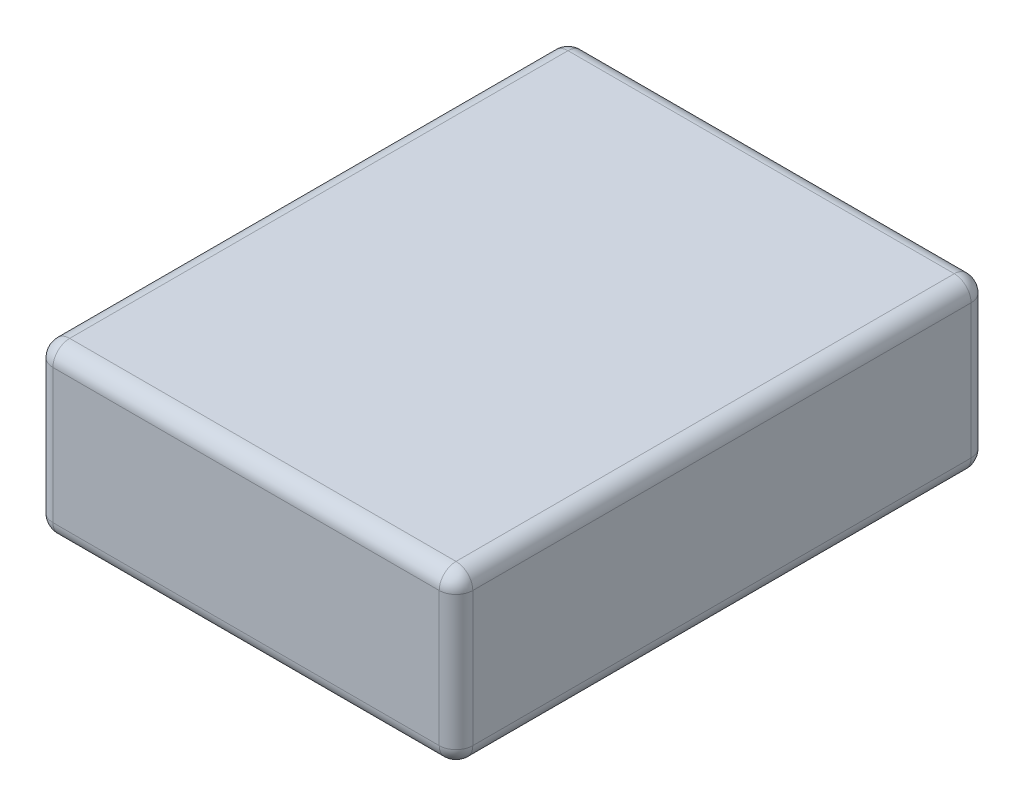
SolidWorks part; units mm, degrees
ref_plane "Спереди" through (0, 0, 0) normal (0, 0, 1) x (1, 0, 0)
ref_plane "Сверху" through (0, 0, 0) normal (0, 1, 0) x (1, 0, 0)
ref_plane "Справа" through (0, 0, 0) normal (1, 0, 0) x (0, 0, -1)
other "Configuration Table"
sketch "Sketch1" plane through (0, 0, 0) normal (0, 0, 1) x (1, 0, 0)
  line L1 (-3.75, -1.5) -> (3.75, -1.5)
  line L2 (-3.75, -1.5) -> (-3.75, 1.5)
  line L3 (-3.75, 1.5) -> (3.75, 1.5)
  line L4 (3.75, -1.5) -> (3.75, 1.5)
  line L5 (-3.75, -1.5) -> (3.75, 1.5) construction
  line L6 (-3.75, 1.5) -> (3.75, -1.5) construction
  point P0 (0, 0)
  dimension "D1" = 3
  dimension "D2" = 7.5
extrude "Boss-Extrude1" add sketch "Sketch1" along normal blind 9.5
fillet "Fillet1" radius 0.3 12 edges at (-3.75, -1.5, 4.75) (-3.75, 0, 0) (0, -1.5, 0) (3.75, -1.5, 4.75) (3.75, 0, 0) (0, -1.5, 9.5) (-3.75, 0, 9.5) (3.75, 0, 9.5) (3.75, 1.5, 4.75) (0, 1.5, 9.5) (-3.75, 1.5, 4.75) (0, 1.5, 0)
